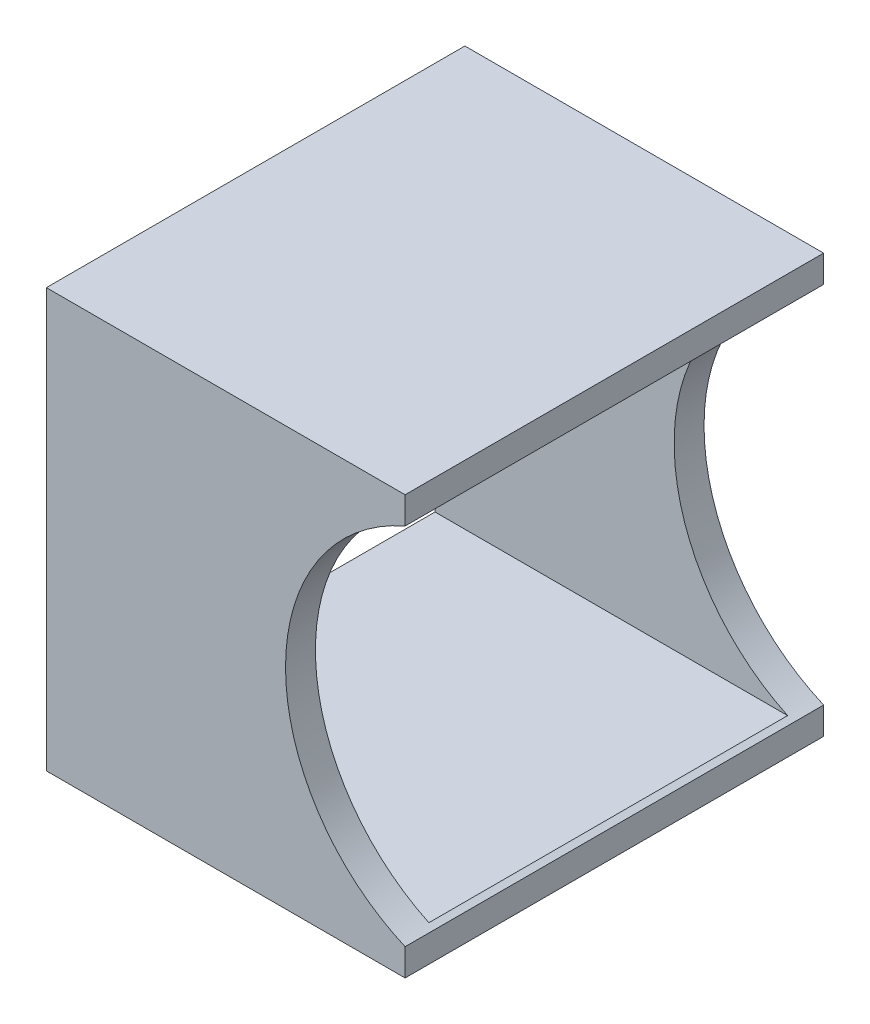
SolidWorks part; units mm, degrees
material "6061 Alloy"
ref_plane "Front Plane" through (0, 0, 0) normal (0, 0, 1) x (1, 0, 0)
ref_plane "Top Plane" through (0, 0, 0) normal (0, 1, 0) x (1, 0, 0)
ref_plane "Right Plane" through (0, 0, 0) normal (1, 0, 0) x (0, 0, -1)
sketch "Sketch1" plane through (0, 0, 0) normal (1, 0, 0) x (0, 0, -1)
  line L1 (0, 0) -> (44.45, 0)
  line L2 (0, 0) -> (0, 44.45)
  line L3 (0, 44.45) -> (44.45, 44.45)
  line L4 (44.45, 0) -> (44.45, 44.45)
  line L5 (3.175, 41.275) -> (41.275, 41.275)
  line L6 (3.175, 41.275) -> (3.175, 3.175)
  line L7 (3.175, 3.175) -> (41.275, 3.175)
  line L8 (41.275, 41.275) -> (41.275, 3.175)
  dimension "D1" = 3.175
  dimension "D2" = 3.175
  dimension "D3" = 44.45
  dimension "D4" = 44.45
  dimension "D5" = 38.1
  dimension "D6" = 38.1
extrude "Boss-Extrude1" add sketch "Sketch1" along normal blind 38.1
sketch "Sketch2" plane through (0, 0, 0) normal (0, 0, 1) x (1, 0, 0)
  line L0 (0, 44.45) -> (0, 0) construction
  line L1 (38.1, 44.45) -> (0, 44.45) construction
  circle A0 centre (46.482, 22.225) radius 21.082
  dimension "D1" = 42.164
  dimension "D2" = 46.482
  dimension "D3" = 22.225
extrude "Cut-Extrude1" cut sketch "Sketch2" against normal through all and the other way through all
